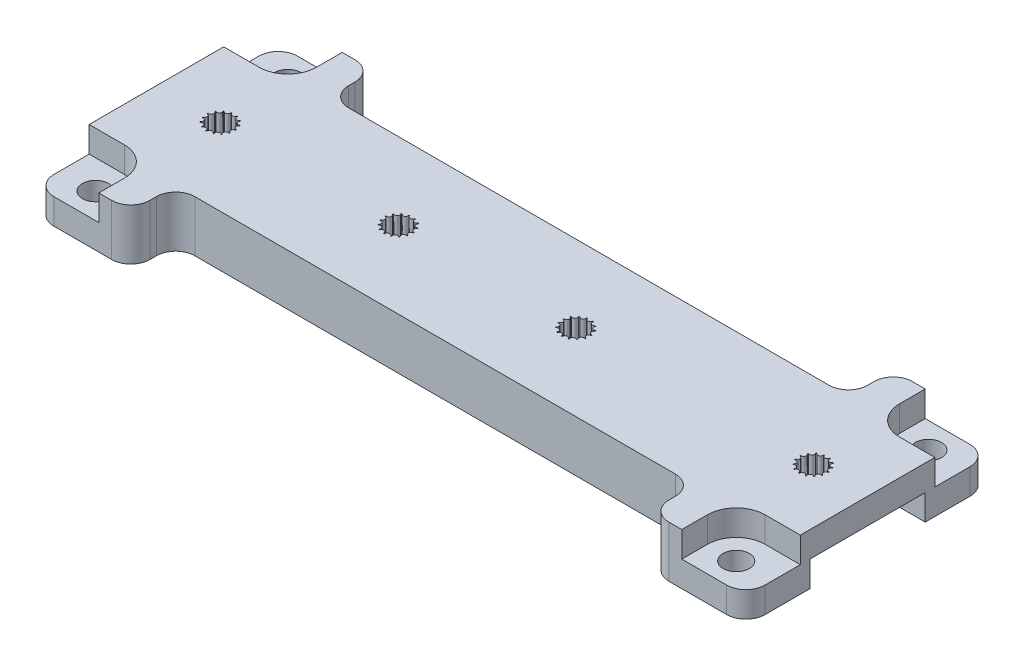
SolidWorks part; units mm, degrees
ref_plane "Front Plane" through (0, 0, 0) normal (0, 0, 1) x (1, 0, 0)
ref_plane "Top Plane" through (0, 0, 0) normal (0, 1, 0) x (1, 0, 0)
ref_plane "Right Plane" through (0, 0, 0) normal (1, 0, 0) x (0, 0, -1)
sketch "Sketch1" plane through (0, 0, 0) normal (0, 1, 0) x (1, 0, 0)
  line L0 (-10, 28) -> (117, 28)
  line L1 (0, 0) -> (107, 0)
  line L2 (0, 0) -> (0, 18)
  line L3 (0, 18) -> (107, 18)
  line L4 (107, 0) -> (107, 18)
  line L5 (117, -10) -> (117, 28)
  line L6 (-10, -10) -> (117, -10)
  line L7 (-10, -10) -> (-10, 28)
  dimension "D1" = 107
  dimension "D2" = 18
  dimension "D3" = 10
extrude "Boss-Extrude1" add sketch "Sketch1" along normal blind 8 contours L0 L5 L6 L7
sketch "Sketch2" plane through (0, 8, 0) normal (0, 1, 0) x (1, 0, 0)
  line L0 (107, 0) -> (107, 18) construction
  line L1 (0, 18) -> (107, 18) construction
  line L2 (0, 0) -> (0, 18) construction
  line L3 (0, 0) -> (107, 0) construction
  line L4 (107, 0) -> (107, 18) construction
  line L5 (0, 18) -> (107, 18) construction
  line L6 (0, 0) -> (0, 18) construction
  line L7 (0, 0) -> (107, 0) construction
  line L8 (-10, -10) -> (-10, 28) construction
  line L9 (-10, 28) -> (117, 28) construction
  circle A0 centre (3.5, 24) radius 2.05
  circle A1 centre (3.5, 24) radius 4.5
  dimension "D1" = 4.1
  dimension "D4" = 9
  dimension "D2" = 13.5
  dimension "D3" = 4
extrude "Cut-Extrude1" cut sketch "Sketch2" against normal blind 10 contours A0
sketch "Sketch3" plane through (0, 8, 0) normal (0, 1, 0) x (1, 0, 0)
  line L0 (8, 24) -> (8, 28)
  line L1 (-10, 28) -> (117, 28) construction
  line L2 (8, 28) -> (-10, 28)
  line L3 (-10, 28) -> (-10, 19.5)
  line L4 (-10, -10) -> (-10, 28) construction
  line L5 (-10, 19.5) -> (3.5, 19.5)
  arc A0 (3.5, 19.5) -> (8, 24) centre (3.5, 24) ccw
  dimension "D1" = 9
extrude "Cut-Extrude2" cut sketch "Sketch3" against normal blind 4
ref_plane "Plane1" through (53.5, 0, 0) normal (-1, 0, 0) x (0, 0, 1)
ref_plane "Plane2" through (0, 0, -9) normal (0, 0, 1) x (1, 0, 0)
mirror "Mirror1" about plane through (53.5, 0, 0) normal (-1, 0, 0) of "Cut-Extrude2", "Cut-Extrude1"
mirror "Mirror2" about plane through (0, 0, -9) normal (0, 0, 1) of "Cut-Extrude2", "Cut-Extrude1", "Mirror1"
sketch "Sketch5" plane through (0, 0, 0) normal (0, -1, 0) x (1, 0, 0)
  line L0 (-10, -28) -> (117, -28) construction
  line L1 (117, -31) -> (-10, -31)
  line L2 (117, -31) -> (117, 13)
  line L3 (117, 13) -> (-10, 13)
  line L4 (-10, -31) -> (-10, 13)
  line L5 (-10, 10) -> (117, 10) construction
  circle A0 centre (103.5, 6) radius 2.05 construction
  circle A1 centre (103.5, -24) radius 2.05 construction
  circle A2 centre (3.5, 6) radius 2.05 construction
  circle A3 centre (3.5, -24) radius 2.05 construction
  circle A4 centre (103.5, 6) radius 2.05
  circle A5 centre (103.5, -24) radius 2.05
  circle A6 centre (3.5, 6) radius 2.05
  circle A7 centre (3.5, -24) radius 2.05
  dimension "D1" = 3
  dimension "D2" = 3
extrude "Boss-Extrude2" add sketch "Sketch5" against normal up to surface (4 mm away) up to face at (103.5, 4, -21.95)
sketch "Sketch6" plane through (0, 4, 0) normal (0, 1, 0) x (1, 0, 0)
  line L0 (117, -13) -> (-10, -13) construction
  line L1 (-2, -13) -> (109, -13)
  line L2 (-2, -13) -> (-2, 31)
  line L3 (-2, 31) -> (109, 31)
  line L4 (109, -13) -> (109, 31)
  line L5 (-10, 31) -> (117, 31) construction
  line L6 (107, 0) -> (107, 18) construction
  line L7 (0, 0) -> (0, 18) construction
  line L9 (-20.3932, -32.0112) -> (125.6297, -32.0112)
  line L10 (-20.3932, -32.0112) -> (-20.3932, 50.64)
  line L11 (-20.3932, 50.64) -> (125.6297, 50.64)
  line L12 (125.6297, -32.0112) -> (125.6297, 50.64)
  dimension "D1" = 2
  dimension "D2" = 2
extrude "Cut-Extrude3" cut sketch "Sketch6" against normal mid plane 24
sketch "Sketch7" plane through (0, 8, 0) normal (0, 1, 0) x (1, 0, 0)
  line L0 (-4.4, 9) -> (4.4, 9) construction
  line L1 (0, 0) -> (0, 18) construction
  line L2 (8, 11.25) -> (8, 5.9533) construction
  circle A0 centre (8, 9) radius 2.25
  circle A1 centre (8, 11.25) radius 0.4
  circle A2 centre (8.9152, 11.0555) radius 0.4
  circle A3 centre (9.6721, 10.5055) radius 0.4
  circle A4 centre (10.1399, 9.6953) radius 0.4
  circle A5 centre (10.2377, 8.7648) radius 0.4
  circle A6 centre (9.9486, 7.875) radius 0.4
  circle A7 centre (9.3225, 7.1797) radius 0.4
  circle A8 centre (8.4678, 6.7992) radius 0.4
  circle A9 centre (7.5322, 6.7992) radius 0.4
  circle A10 centre (6.6775, 7.1797) radius 0.4
  circle A11 centre (6.0514, 7.875) radius 0.4
  circle A12 centre (5.7623, 8.7648) radius 0.4
  circle A13 centre (5.8601, 9.6953) radius 0.4
  circle A14 centre (6.3279, 10.5055) radius 0.4
  circle A15 centre (7.0848, 11.0555) radius 0.4
  point P39 (8, 9)
  dimension "D1" = 4.5
  dimension "D3" = 0.8
  dimension "D2" = 8
  dimension "D4" = 15
extrude "Cut-Extrude4" cut sketch "Sketch7" against normal mid plane 24 contours L2 A1 A0 A15 A14 A13 A12 A11 A10 A9 | A1 L2 A0 A8 A7 A6 A5 A4 A3 A2
pattern_linear "LPattern1" count 11 spacing 9.25 along (1, 0, 0) skipping (1, 0), (2, 0), (4, 0), (5, 0), (7, 0), (8, 0), (9, 0) of "Cut-Extrude4"
sketch "Sketch8" plane through (0, 0, 0) normal (0, -1, 0) x (1, 0, 0)
  line L0 (0, 0) -> (0, -18) construction
  line L1 (0, -18) -> (107, -18) construction
  line L2 (0, 0) -> (107, 0) construction
  line L3 (107, 0) -> (107, -18) construction
  line L4 (0, 0) -> (0, -18)
  line L5 (0, -18) -> (107, -18)
  line L6 (0, 0) -> (107, 0)
  line L7 (107, 0) -> (107, -18)
  line L8 (3, 0) -> (3, -18)
  line L9 (104, 0) -> (104, -18)
  line L11 (111.1598, 0) -> (-3.8846, 0)
  line L12 (111.1598, 0) -> (111.1598, -18)
  line L13 (111.1598, -18) -> (-3.8846, -18)
  line L14 (-3.8846, 0) -> (-3.8846, -18)
  dimension "D1" = 3
  dimension "D2" = 3
extrude "Cut-Extrude5" cut sketch "Sketch8" against normal blind 4 contours L9 L6 L8 L5 | L13 L12 L11 L7 | L6 L9 L5 L7 | L11 L14 L13 L4 | L8 L6 L4 L5
sketch "Sketch9" plane through (0, 4, 0) normal (0, 1, 0) x (1, 0, 0)
  line L0 (53.5, -13) -> (53.5, 31) construction
  line L1 (109, -13) -> (-2, -13) construction
  line L2 (-2, 31) -> (109, 31) construction
  line L3 (109, 19.5) -> (109, 31) construction
  line L4 (94, 31) -> (13, 31)
  line L5 (94, 31) -> (94, 21)
  line L6 (94, 21) -> (13, 21)
  line L7 (13, 31) -> (13, 21)
  line L8 (-2, 31) -> (-2, 19.5) construction
  dimension "D1" = 15
  dimension "D2" = 15
  dimension "D3" = 10
extrude "Cut-Extrude6" cut sketch "Sketch9" against normal mid plane 20
mirror "Mirror3" about plane through (0, 0, -9) normal (0, 0, 1) of "Cut-Extrude6"
sketch "Sketch10" plane through (0, 4, 0) normal (0, 1, 0) x (1, 0, 0)
  line L0 (-10, -10) -> (-10, 28) construction
  line L1 (125.2422, 39.1256) -> (-17.0098, 39.1256)
  line L2 (125.2422, 39.1256) -> (125.2422, -16.4373)
  line L3 (125.2422, -16.4373) -> (-17.0098, -16.4373)
  line L4 (-17.0098, 39.1256) -> (-17.0098, -16.4373)
  line L5 (-10, 28) -> (117, 28) construction
  line L6 (117, -10) -> (117, 28) construction
  line L7 (-10, -10) -> (117, -10) construction
  line L8 (-10, -10) -> (-10, 28)
  line L9 (-10, 28) -> (117, 28)
  line L10 (117, -10) -> (117, 28)
  line L11 (-10, -10) -> (117, -10)
extrude "Cut-Extrude7" cut sketch "Sketch10" against normal blind 10
fillet "Fillet1" radius 3 12 edges at (13, 4, 3) (94, 4, 3) (109, 2, -28) (109, 2, 10) (-2, 2, 10) (-2, 2, -28) (13, 4, -28) (94, 4, -28) (94, 4, -21) (13, 4, -21) (13, 4, 10) (94, 4, 10)
